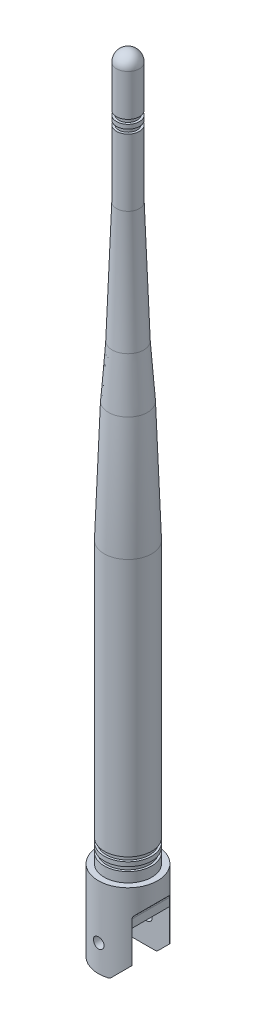
SolidWorks part; units mm, degrees
ref_plane "Front Plane" through (0, 0, 0) normal (0, 0, 1) x (1, 0, 0)
ref_plane "Top Plane" through (0, 0, 0) normal (0, 1, 0) x (1, 0, 0)
ref_plane "Right Plane" through (0, 0, 0) normal (1, 0, 0) x (0, 0, -1)
sketch "Sketch1" plane through (0, 0, 0) normal (0, 0, 1) x (1, 0, 0)
  line L0 (0, 0) -> (-5.6, 0)
  line L1 (-5.6, 0) -> (-5.6, 2.32)
  line L2 (-5.6, 2.32) -> (-5.095, 2.32)
  line L3 (-5.095, 2.32) -> (-5.095, 3.32)
  line L4 (-5.095, 3.32) -> (-5.6, 3.32)
  line L5 (-5.6, 3.32) -> (-5.6, 4.32)
  line L6 (-5.6, 4.32) -> (-5.095, 4.32)
  line L7 (-5.095, 4.32) -> (-5.095, 5.32)
  line L8 (-5.095, 5.32) -> (-5.6, 5.32)
  line L9 (0, 0) -> (0, 328.9667) construction
  line L10 (-5.6, 5.32) -> (-5.6, 66.1049)
  line L11 (-3.7141, 106.8208) -> (-4.5909, 94.4992)
  line L12 (-2.705, 151) -> (-2.705, 135.2151)
  line L13 (-2.705, 151) -> (-2.17, 151)
  line L14 (-2.17, 151) -> (-2.17, 152)
  line L15 (-2.17, 152) -> (-2.705, 152)
  line L16 (-2.705, 152) -> (-2.705, 153)
  line L17 (-2.705, 153) -> (-2.17, 153)
  line L18 (-2.17, 153) -> (-2.17, 154)
  line L19 (-2.17, 154) -> (-2.705, 154)
  line L20 (-2.705, 154) -> (-2.705, 163.795)
  line L21 (-2.705, 163.795) -> (0, 163.795) construction
  line L22 (-5.095, 2.32) -> (-5.095, 5.32) construction
  line L23 (-2.17, 151) -> (-2.17, 154) construction
  line L24 (0, 0) -> (0, 166.5)
  arc A0 (-2.705, 163.795) -> (0, 166.5) centre (0, 163.795) cw
  arc A1 (-5.6, 66.1049) -> (-4.5909, 94.4992) centre (394.4, 66.1049) cw
  arc A2 (-2.705, 135.2151) -> (-3.7141, 106.8208) centre (-402.705, 135.2151) cw
  point P26 (-5.6, 80.32)
  point P30 (-2.705, 121)
  dimension "D16" = 400
  dimension "D1" = 5.6
  dimension "D2" = 2.705
  dimension "D3" = 5.095
  dimension "D4" = 2.17
  dimension "D5" = 12.5
  dimension "D6" = 1
  dimension "D7" = 1
  dimension "D8" = 1
  dimension "D9" = 1
  dimension "D10" = 1
  dimension "D11" = 1
  dimension "D12" = 5.32
  dimension "D13" = 154
  dimension "D14" = 75
  dimension "D15" = 30
revolve "Revolve1" add sketch "Sketch1" angle 360 about L9
sketch "Sketch3" plane through (0, 0, 0) normal (0, -1, 0) x (1, 0, 0)
  circle A0 centre (0, 0) radius 7
  dimension "D1" = 14
extrude "Boss-Extrude1" add sketch "Sketch3" along normal blind 19
sketch "Sketch4" plane through (0, 0, 0) normal (1, 0, 0) x (0, 0, -1)
  line L0 (-7, -19) -> (7, -19) construction
  line L1 (-4.46, -19) -> (4.46, -19)
  line L2 (-4.46, -19) -> (-4.46, -8.3)
  line L3 (-4.46, -8.3) -> (4.46, -8.3)
  line L4 (4.46, -19) -> (4.46, -8.3)
  line L5 (7, 0) -> (-7, 0) construction
  line L6 (7, -19) -> (7, 0) construction
  line L7 (7, -19) -> (7, 0) construction
  line L8 (-7, -19) -> (-7, 0) construction
  dimension "D1" = 8.3
  dimension "D2" = 2.54
  dimension "D3" = 2.54
extrude "Cut-Extrude1" cut sketch "Sketch4" against normal blind 4.46 and the other way blind 9
sketch "Sketch5" plane through (0, 0, 0) normal (0, 0, 1) x (1, 0, 0)
  line L0 (5.3952, -6) -> (5.3952, -15.934)
  line L1 (5.3952, -6) -> (9.0165, -2.3787)
  line L2 (9.0165, -2.3787) -> (9.0165, -20.5445)
  line L3 (9.0165, -20.5445) -> (0.7847, -20.5445)
  line L4 (0.7847, -20.5445) -> (5.3952, -15.934)
  line L5 (5.3952, -8.3) -> (5.3952, -19) construction
  line L6 (-4.46, -19) -> (5.3952, -19) construction
  circle A0 centre (0, -12.7) radius 1.25
  point P2 (0.4676, -19)
  dimension "D1" = 2.5
  dimension "D2" = 13
  dimension "D3" = 45
  dimension "D4" = 45
  dimension "D5" = 6.3
extrude "Cut-Extrude2" cut sketch "Sketch5" against normal blind 14.46 and the other way blind 14.46
fillet "Fillet1" radius 1 5 edges at (5.3952, -6, 0) (2.3292, -19, -5.5306) (2.3292, -19, 5.5306) (-4.46, -13.65, -4.46) (-4.46, -13.65, 4.46)
